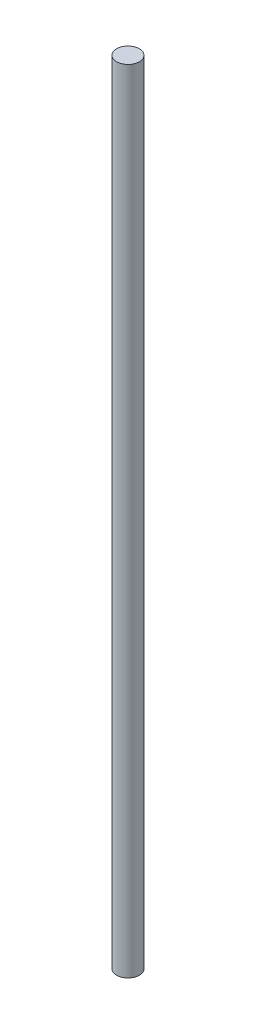
SolidWorks part; units mm, degrees
ref_plane "Front Plane" through (0, 0, 0) normal (0, 0, 1) x (1, 0, 0)
ref_plane "Top Plane" through (0, 0, 0) normal (0, 1, 0) x (1, 0, 0)
ref_plane "Right Plane" through (0, 0, 0) normal (1, 0, 0) x (0, 0, -1)
sketch "Sketch2" plane through (0, 0, 0) normal (0, 1, 0) x (1, 0, 0)
  circle A0 centre (0, 0) radius 2
extrude "Boss-Extrude1" add sketch "Sketch2" along normal blind 140
